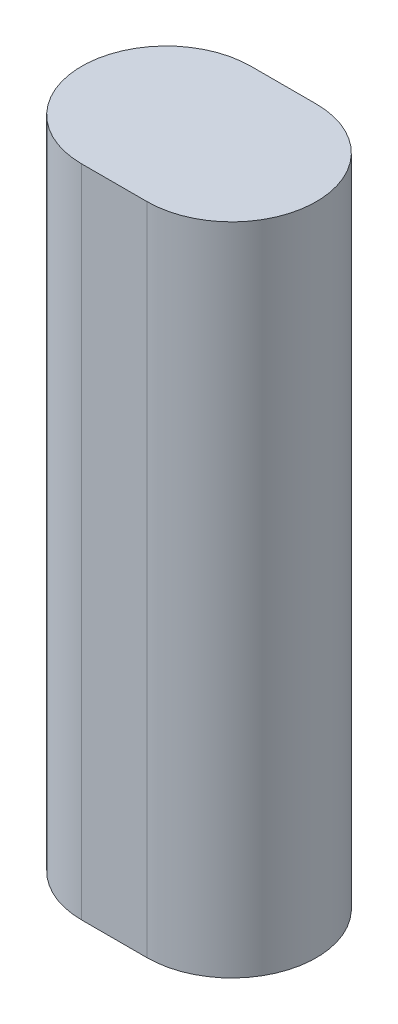
SolidWorks part; units mm, degrees
material "Alumina"
ref_plane "Front Plane" through (0, 0, 0) normal (0, 0, 1) x (1, 0, 0)
ref_plane "Top Plane" through (0, 0, 0) normal (0, 1, 0) x (1, 0, 0)
ref_plane "Right Plane" through (0, 0, 0) normal (1, 0, 0) x (0, 0, -1)
sketch "Sketch1" plane through (0, 0, 0) normal (0, 1, 0) x (1, 0, 0)
  line L0 (0, 0) -> (12, 0) construction
  line L1 (0, 15.5) -> (12, 15.5)
  line L2 (0, -15.5) -> (12, -15.5)
  arc A0 (0, 15.5) -> (0, -15.5) centre (0, 0) ccw
  arc A1 (12, -15.5) -> (12, 15.5) centre (12, 0) ccw
  point P3 (6, 0)
  point P8 (-15.5, 0)
  point P9 (27.5, 0)
  dimension "D2" = 43
  dimension "D1" = 31
extrude "Boss-Extrude2" add sketch "Sketch1" along normal blind 120 contours A1 L1 A0 L2
